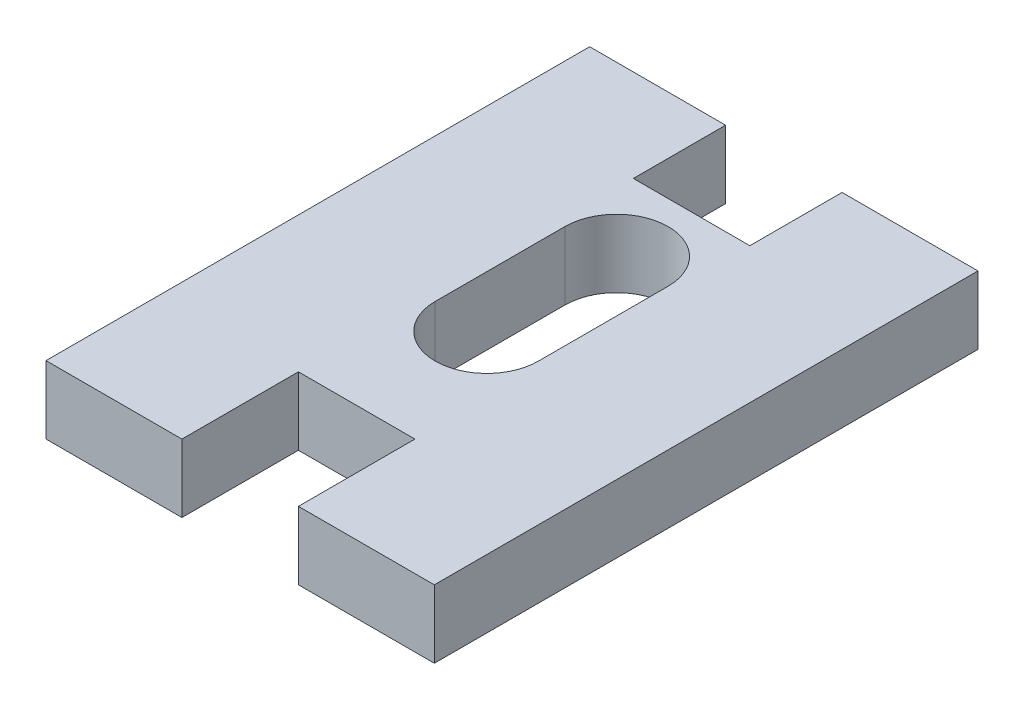
SolidWorks part; units mm, degrees
ref_plane "Front Plane" through (0, 0, 0) normal (0, 0, 1) x (1, 0, 0)
ref_plane "Top Plane" through (0, 0, 0) normal (0, 1, 0) x (1, 0, 0)
ref_plane "Right Plane" through (0, 0, 0) normal (1, 0, 0) x (0, 0, -1)
sketch "Sketch1" plane through (0, 0, 0) normal (0, 1, 0) x (1, 0, 0)
  line L1 (0, 0) -> (20, 0)
  line L2 (0, 0) -> (0, 28)
  line L3 (0, 28) -> (20, 28)
  line L4 (20, 0) -> (20, 28)
  dimension "D1" = 28
  dimension "D2" = 20
extrude "Boss-Extrude1" add sketch "Sketch1" along normal blind 3.5
sketch "Sketch2" plane through (0, 3.5, 0) normal (0, 1, 0) x (1, 0, 0)
  line L0 (20, 28) -> (0, 28) construction
  line L1 (7, 28) -> (13, 28)
  line L2 (7, 28) -> (7, 23.25)
  line L3 (7, 23.25) -> (13, 23.25)
  line L4 (13, 28) -> (13, 23.25)
  line L5 (0, 0) -> (20, 0) construction
  line L6 (7, 0) -> (13, 0)
  line L7 (7, 0) -> (7, 6)
  line L8 (7, 6) -> (13, 6)
  line L9 (13, 0) -> (13, 6)
  point P14 (10, 28)
  point P15 (10, 28)
  point P16 (10, 0)
  point P17 (10, 0)
  dimension "D1" = 6
  dimension "D2" = 6
  dimension "D3" = 6
  dimension "D4" = 4.75
extrude "Cut-Extrude1" cut sketch "Sketch2" against normal through all
sketch "Sketch4" plane through (0, 3.5, 0) normal (0, 1, 0) x (1, 0, 0)
  line L0 (10.043, 19.34) -> (10.043, 12.66) construction
  line L1 (12.703, 19.34) -> (12.703, 12.66)
  line L2 (7.383, 19.34) -> (7.383, 12.66)
  line L3 (20, 28) -> (13, 28) construction
  arc A0 (12.703, 19.34) -> (7.383, 19.34) centre (10.043, 19.34) ccw
  arc A1 (7.383, 12.66) -> (12.703, 12.66) centre (10.043, 12.66) ccw
  point P2 (10.043, 16)
  point P10 (10.043, 10)
  point P11 (10.043, 22)
  dimension "D1" = 12
  dimension "D2" = 5.32
  dimension "D3" = 6
extrude "Cut-Extrude6" cut sketch "Sketch4" against normal through all
